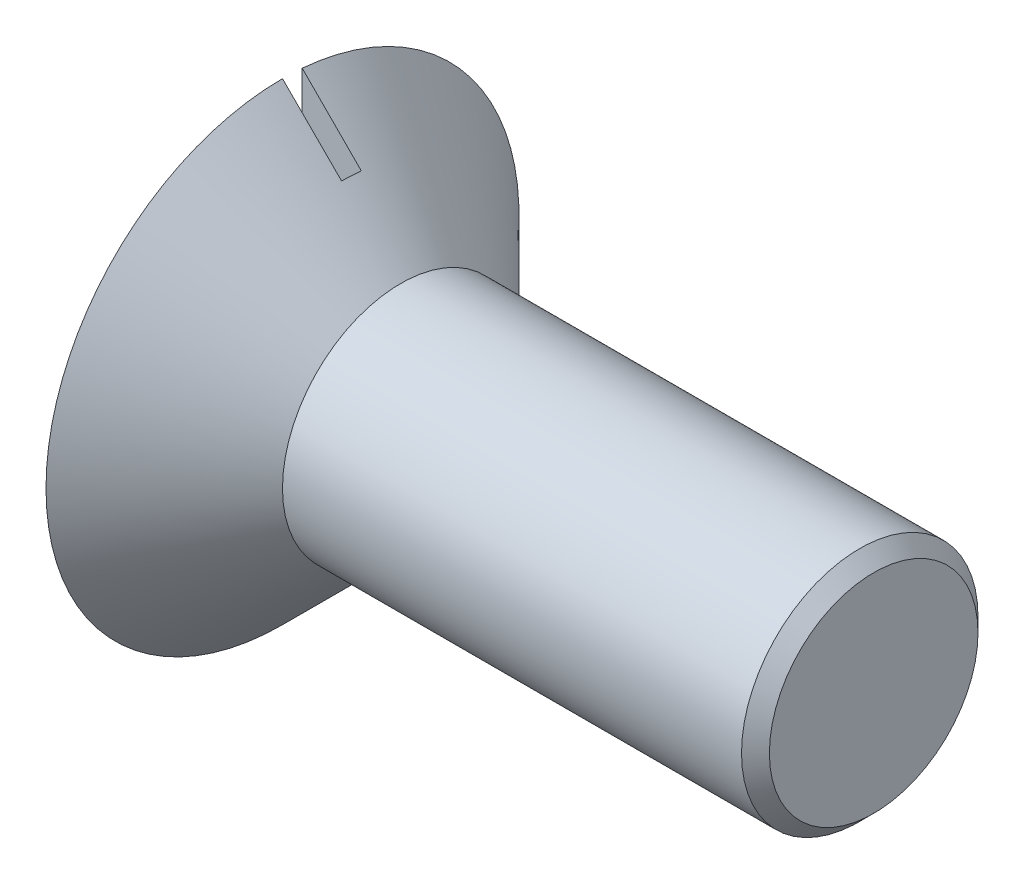
SolidWorks part; units mm, degrees
ref_plane "Front Plane" through (0, 0, 0) normal (0, 0, 1) x (1, 0, 0)
ref_plane "Top Plane" through (0, 0, 0) normal (0, 1, 0) x (1, 0, 0)
ref_plane "Right Plane" through (0, 0, 0) normal (1, 0, 0) x (0, 0, -1)
sketch "Sketch2" plane through (0, 0, 0) normal (0, 0, 1) x (1, 0, 0)
  line L0 (-22.0003, 0) -> (60.2695, 0) construction
  line L1 (10.4415, 6) -> (25.22, 6)
  line L2 (25.22, 6) -> (33.7344, 6)
  line L3 (34.4415, 5.2929) -> (34.4415, 2.7886)
  line L4 (10.4415, 6) -> (4.4415, 12)
  line L5 (4.4415, 12) -> (4.4415, 0)
  line L6 (34.4415, 2.7886) -> (34.4415, 0)
  line L7 (34.4415, 5.2929) -> (33.7344, 6)
  line L10 (4.4415, 0) -> (34.4415, 0)
  dimension "D2" = 30
  dimension "D3" = 6
  dimension "D4" = 1
  dimension "D5" = 45
  dimension "D6" = 6
revolve "Revolve1" add sketch "Sketch2" angle 360 about L0
sketch "Sketch3" plane through (0, 0, 0) normal (0, 1, 0) x (1, 0, 0)
  line L0 (4.4415, 1.001) -> (7.4415, 1.001)
  line L1 (4.4415, 12) -> (4.4415, -12) construction
  line L2 (7.4415, 1.001) -> (7.4415, 0)
  line L3 (7.4415, 0) -> (4.4415, 0)
  line L4 (4.4415, 0) -> (4.4415, 1.001)
  dimension "D1" = 1.001
  dimension "D2" = 3
extrude "Cut-Extrude1" cut sketch "Sketch3" against normal mid plane 100
